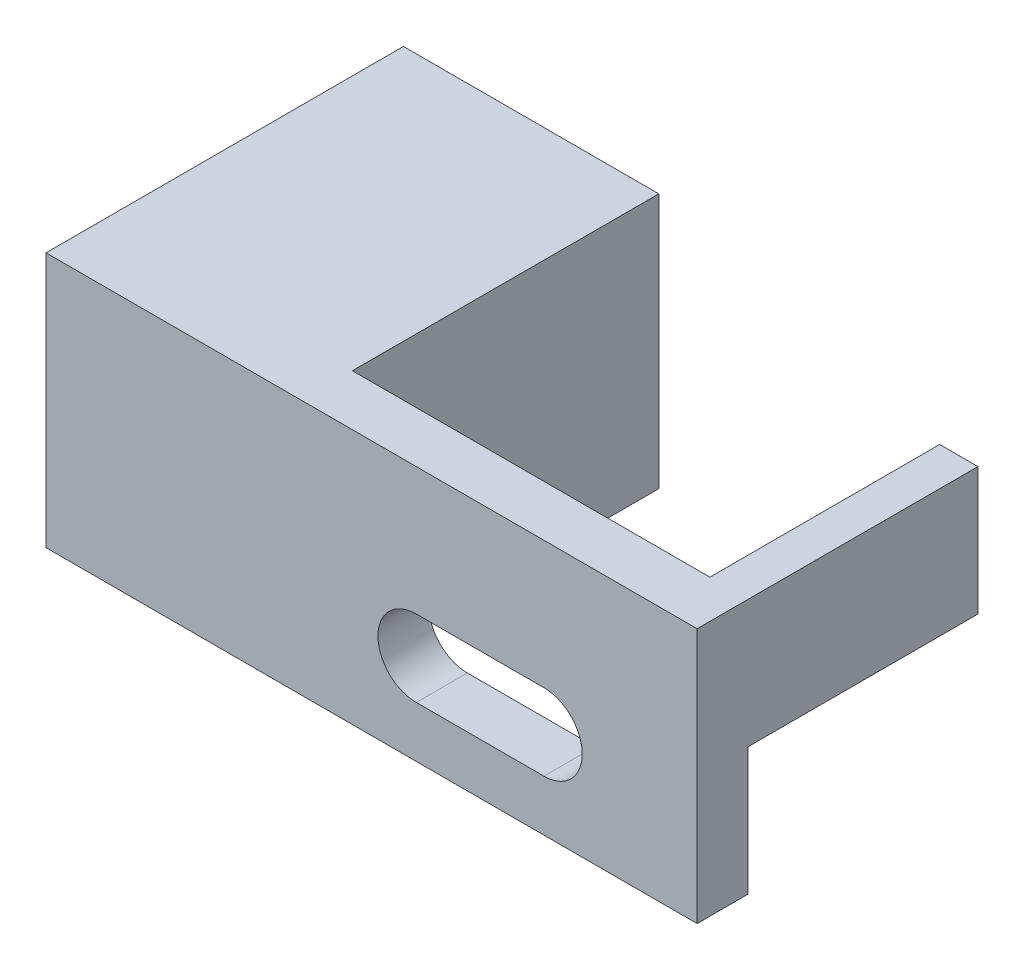
SolidWorks part; units mm, degrees
ref_plane "Front Plane" through (0, 0, 0) normal (0, 0, 1) x (1, 0, 0)
ref_plane "Top Plane" through (0, 0, 0) normal (0, 1, 0) x (1, 0, 0)
ref_plane "Right Plane" through (0, 0, 0) normal (1, 0, 0) x (0, 0, -1)
sketch "Sketch1" plane through (0, 0, 0) normal (0, 1, 0) x (1, 0, 0)
  line L0 (0, 0) -> (25.5, 0)
  line L4 (25.5, 0) -> (25.5, 11)
  line L5 (25.5, 11) -> (24, 11)
  line L6 (24, 11) -> (24, 2)
  line L7 (24, 2) -> (10, 2)
  line L8 (10, 2) -> (10, 14)
  line L9 (10, 14) -> (0, 14)
  line L10 (0, 14) -> (0, 0)
  dimension "D1" = 2
  dimension "D2" = 1.5
  dimension "D3" = 3
  dimension "D4" = 14
  dimension "D5" = 10
  dimension "D6" = 25.5
  dimension "D7" = 9
extrude "Boss-Extrude1" add sketch "Sketch1" along normal blind 10
sketch "Sketch2" plane through (24, 0, 0) normal (-1, 0, 0) x (0, 0, 1)
  line L0 (-11, 5) -> (-2, 5)
  line L1 (-11, 10) -> (-11, 0) construction
  line L2 (-2, 10) -> (-2, 0) construction
  line L3 (-2, 5) -> (-2, 0)
  line L4 (-2, 0) -> (-11, 0)
  line L5 (-11, 0) -> (-11, 5)
extrude "Cut-Extrude1" cut sketch "Sketch2" against normal up to next
sketch "Sketch3" plane through (0, 0, -2) normal (0, 0, -1) x (-1, 0, 0)
  line L0 (-19.5, 5) -> (-14.5, 5)
  line L1 (-19.5, 2) -> (-14.5, 2)
  line L4 (-24, 5) -> (-24, 0) construction
  line L5 (-25.5, 0) -> (-10, 0) construction
  line L7 (-24, 3.5) -> (-21, 3.5) construction
  line L8 (-13, 3.5) -> (-10, 3.5) construction
  line L9 (-10, 10) -> (-10, 0) construction
  line L10 (-25.5, 5) -> (-24, 5) construction
  arc A0 (-19.5, 5) -> (-19.5, 2) centre (-19.5, 3.5) ccw
  arc A1 (-14.5, 2) -> (-14.5, 5) centre (-14.5, 3.5) ccw
  dimension "D2" = 3
  dimension "D1" = 5
extrude "Cut-Extrude2" cut sketch "Sketch3" against normal up to next
